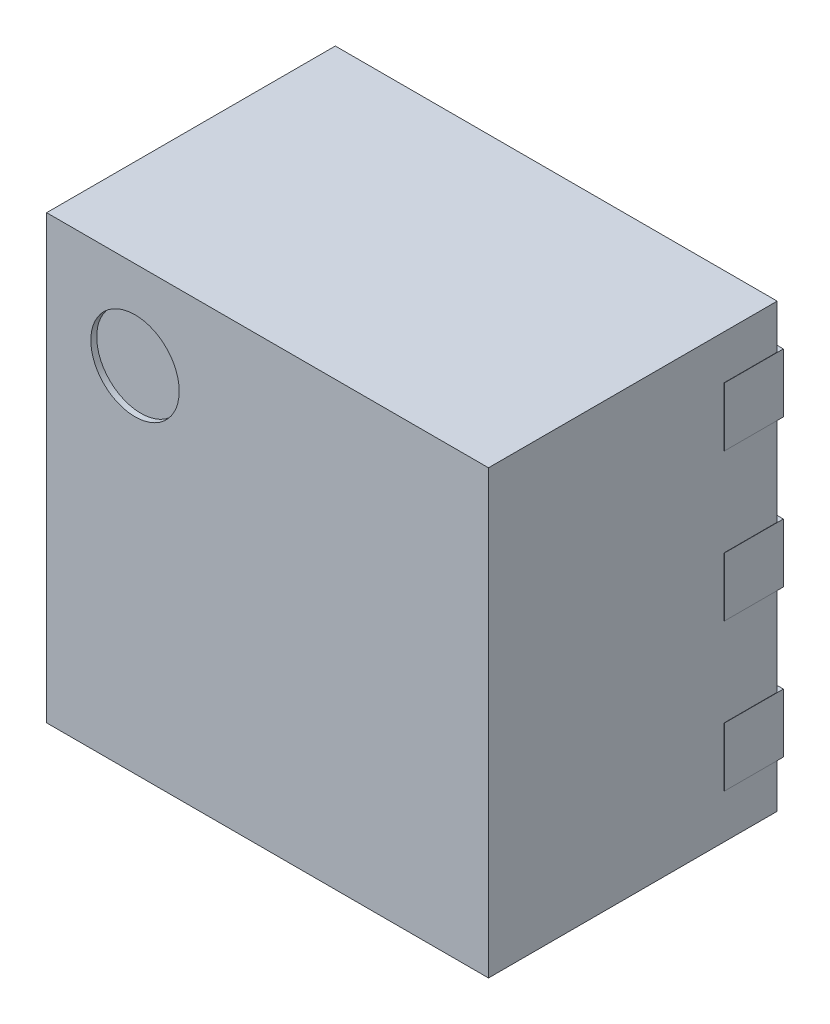
SolidWorks part; units mm, degrees
ref_plane "Front Plane" through (0, 0, 0) normal (0, 0, 1) x (1, 0, 0)
ref_plane "Top Plane" through (0, 0, 0) normal (0, 1, 0) x (1, 0, 0)
ref_plane "Right Plane" through (0, 0, 0) normal (1, 0, 0) x (0, 0, -1)
sketch "Sketch1" plane through (0, 0, 0) normal (0, 0, 1) x (1, 0, 0)
  line L1 (-0.75, 0.75) -> (0.75, 0.75)
  line L2 (-0.75, 0.75) -> (-0.75, -0.75)
  line L3 (-0.75, -0.75) -> (0.75, -0.75)
  line L4 (0.75, 0.75) -> (0.75, -0.75)
  line L5 (-0.75, 0.75) -> (0.75, -0.75) construction
  line L6 (-0.75, -0.75) -> (0.75, 0.75) construction
  point P0 (0, 0)
  dimension "D1" = 1.5
  dimension "D2" = 1.5
extrude "Boss-Extrude1" add sketch "Sketch1" along normal blind 0.98
sketch "Sketch2" plane through (0, 0, 0.98) normal (0, 0, 1) x (1, 0, 0)
  line L0 (-0.75, 0.75) -> (0.75, -0.75) construction
  line L1 (0.75, 0.75) -> (-0.75, 0.75) construction
  circle A0 centre (-0.45, 0.45) radius 0.15
  dimension "D2" = 0.3
  dimension "D1" = 0.3
extrude "Cut-Extrude1" cut sketch "Sketch2" against normal blind 0.02
ref_plane "Plane4" through (0, 0, -0.02) normal (0, 0, 1) x (1, 0, 0)
sketch "Sketch3" plane through (0, 0, -0.02) normal (0, 0, 1) x (1, 0, 0)
  line L0 (0.751, 0.5) -> (-0.751, 0.5) construction
  line L1 (1.0323, 0) -> (-0.751, 0) construction
  line L2 (0.751, -0.5) -> (-0.751, -0.5) construction
  line L3 (-0.751, 0.625) -> (-0.751, 0.375)
  line L4 (-0.751, 0.375) -> (-0.475, 0.375)
  line L5 (-0.751, 0.625) -> (-0.475, 0.625)
  line L6 (-0.75, 0.75) -> (-0.75, -0.75) construction
  line L7 (-0.751, -0.625) -> (-0.475, -0.625)
  line L8 (-0.751, -0.625) -> (-0.751, -0.375)
  line L9 (-0.751, -0.375) -> (-0.475, -0.375)
  line L10 (-0.751, 0.125) -> (-0.751, -0.125)
  line L11 (-0.751, -0.125) -> (-0.475, -0.125)
  line L12 (-0.751, 0.125) -> (-0.475, 0.125)
  line L13 (0.751, 0.6) -> (0.751, 0.4)
  line L14 (0.751, 0.6) -> (0.05, 0.6)
  line L15 (0.751, 0.4) -> (0.05, 0.4)
  line L16 (0.75, -0.75) -> (0.75, 0.75) construction
  line L17 (0.751, -0.6) -> (0.05, -0.6)
  line L18 (0.751, -0.6) -> (0.751, -0.4)
  line L19 (0.751, -0.4) -> (0.05, -0.4)
  line L20 (0.751, 0.1) -> (0.751, -0.1)
  line L21 (0.751, 0.1) -> (0.05, 0.1)
  line L22 (0.751, -0.1) -> (0.05, -0.1)
  arc A0 (-0.475, 0.625) -> (-0.475, 0.375) centre (-0.475, 0.5) cw
  arc A1 (-0.475, -0.625) -> (-0.475, -0.375) centre (-0.475, -0.5) ccw
  arc A2 (-0.475, 0.125) -> (-0.475, -0.125) centre (-0.475, 0) cw
  arc A3 (0.05, 0.6) -> (0.05, 0.4) centre (0.05, 0.5) ccw
  arc A4 (0.05, -0.6) -> (0.05, -0.4) centre (0.05, -0.5) cw
  arc A5 (0.05, 0.1) -> (0.05, -0.1) centre (0.05, 0) ccw
  point P9 (-0.751, 0.5)
  point P13 (-0.35, 0.5)
  point P23 (-0.751, 0)
  point P27 (-0.6, 0)
  point P32 (0.751, 0.5)
  point P36 (-0.05, 0.5)
  point P46 (0.751, 0)
  point P48 (-0.05, 0)
  point P49 (0, 0)
  point P50 (0, 0)
  point P51 (1.0323, 0)
  dimension "D1" = 0.5
  dimension "D2" = 0.4
  dimension "D3" = 0.001
  dimension "D4" = 0.25
  dimension "D5" = 0.001
  dimension "D6" = 0.8
  dimension "D7" = 0.2
extrude "Boss-Extrude2" add sketch "Sketch3" along normal blind 0.2
